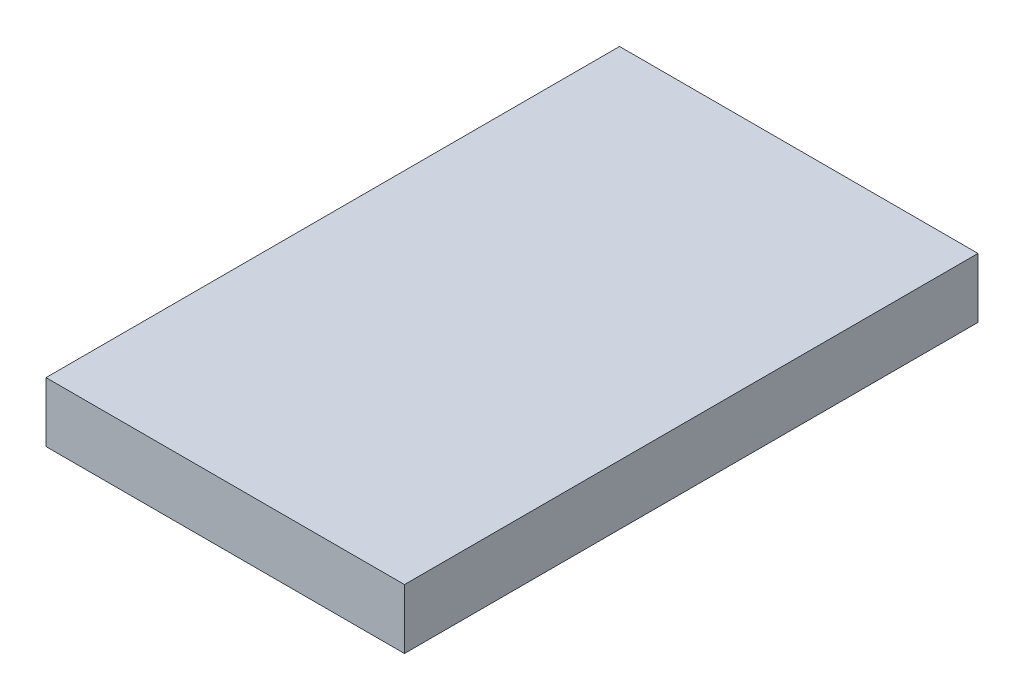
SolidWorks part; units mm, degrees
ref_plane "Front Plane" through (0, 0, 0) normal (0, 0, 1) x (1, 0, 0)
ref_plane "Top Plane" through (0, 0, 0) normal (0, 1, 0) x (1, 0, 0)
ref_plane "Right Plane" through (0, 0, 0) normal (1, 0, 0) x (0, 0, -1)
sketch "Sketch1" plane through (0, 0, 0) normal (0, 1, 0) x (1, 0, 0)
  line L1 (-9.525, -15.24) -> (9.525, -15.24)
  line L2 (-9.525, -15.24) -> (-9.525, 15.24)
  line L3 (-9.525, 15.24) -> (9.525, 15.24)
  line L4 (9.525, -15.24) -> (9.525, 15.24)
  line L5 (-9.525, -15.24) -> (9.525, 15.24) construction
  line L6 (-9.525, 15.24) -> (9.525, -15.24) construction
  point P0 (0, 0)
extrude "Boss-Extrude1" add sketch "Sketch1" along normal blind 3.175
